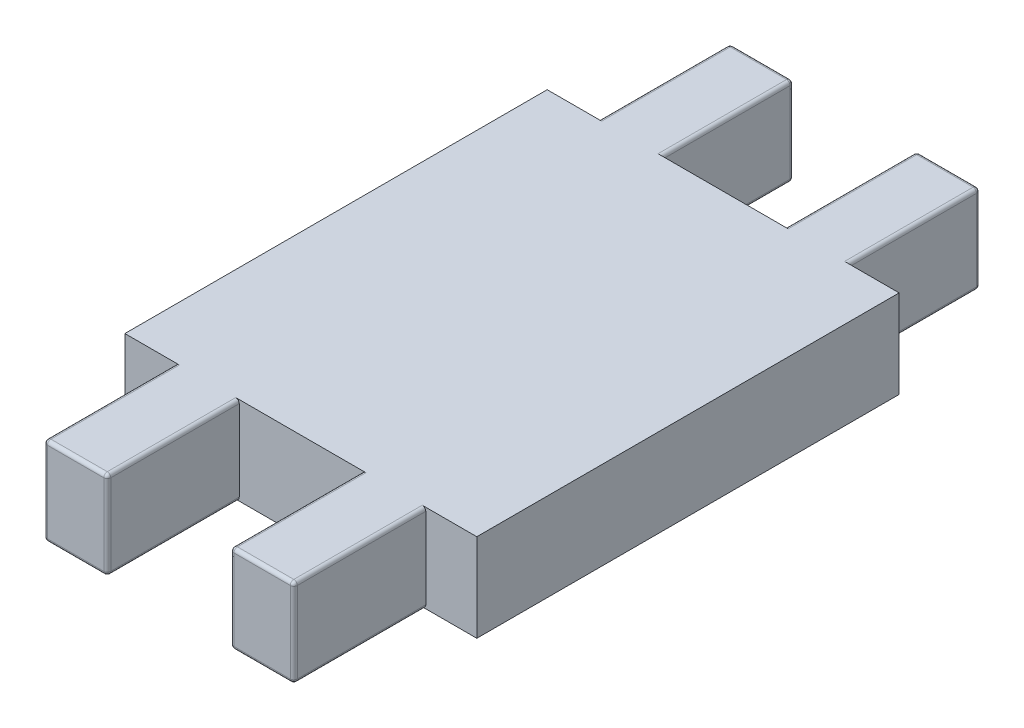
SolidWorks part; units mm, degrees
ref_plane "Front Plane" through (0, 0, 0) normal (0, 0, 1) x (1, 0, 0)
ref_plane "Top Plane" through (0, 0, 0) normal (0, 1, 0) x (1, 0, 0)
ref_plane "Right Plane" through (0, 0, 0) normal (1, 0, 0) x (0, 0, -1)
sketch "Sketch1" plane through (0, 0, 0) normal (0, 1, 0) x (1, 0, 0)
  line L1 (10, -12) -> (-10, -12)
  line L2 (10, -12) -> (10, 12)
  line L3 (10, 12) -> (-10, 12)
  line L4 (-10, -12) -> (-10, 12)
  line L5 (10, -12) -> (-10, 12) construction
  line L6 (10, 12) -> (-10, -12) construction
  point P0 (0, 0)
  dimension "D1" = 24
  dimension "D2" = 20
extrude "Boss-Extrude1" add sketch "Sketch1" along normal mid plane 5
sketch "Sketch2" plane through (0, 2.5, 0) normal (0, 1, 0) x (1, 0, 0)
  line L0 (-10, -12) -> (10, -12) construction
  line L1 (-7.1, -12) -> (-3.5, -12)
  line L2 (-7.1, -12) -> (-7.1, -19.5)
  line L3 (-7.1, -19.5) -> (-3.5, -19.5)
  line L4 (-3.5, -12) -> (-3.5, -19.5)
  line L5 (-10, 12) -> (-10, -12) construction
  dimension "D1" = 7.5
  dimension "D2" = 2.9
  dimension "D3" = 3.6
extrude "Boss-Extrude2" add sketch "Sketch2" against normal blind 5
mirror "Mirror1" about plane through (0, 0, 0) normal (1, 0, 0) of "Boss-Extrude2"
mirror "Mirror2" about plane through (0, 0, 0) normal (0, 0, 1) of "Mirror1", "Boss-Extrude2"
fillet "Fillet1" radius 0.2 32 edges at (7.1, 0, 19.5) (5.3, -2.5, 19.5) (3.5, 0, 19.5) (5.3, 2.5, 19.5) (-3.5, 0, 19.5) (-5.3, 2.5, 19.5) (-5.3, -2.5, 19.5) (-7.1, 0, 19.5) (3.5, 0, -19.5) (5.3, 2.5, -19.5) (5.3, -2.5, -19.5) (7.1, 0, -19.5) (-7.1, 0, -19.5) (-5.3, 2.5, -19.5) (-5.3, -2.5, -19.5) (-3.5, 0, -19.5) (-3.5, 2.5, 15.75) (-3.5, -2.5, 15.75) (-7.1, 2.5, 15.75) (-7.1, -2.5, 15.75) (3.5, -2.5, 15.75) (7.1, 2.5, 15.75) (3.5, 2.5, 15.75) (7.1, -2.5, 15.75) (7.1, 2.5, -15.75) (7.1, -2.5, -15.75) (3.5, 2.5, -15.75) (3.5, -2.5, -15.75) (-7.1, 2.5, -15.75) (-7.1, -2.5, -15.75) (-3.5, 2.5, -15.75) (-3.5, -2.5, -15.75)
scale "Scale1" scale about centroid uniform scaling yes scale factor 0.3
